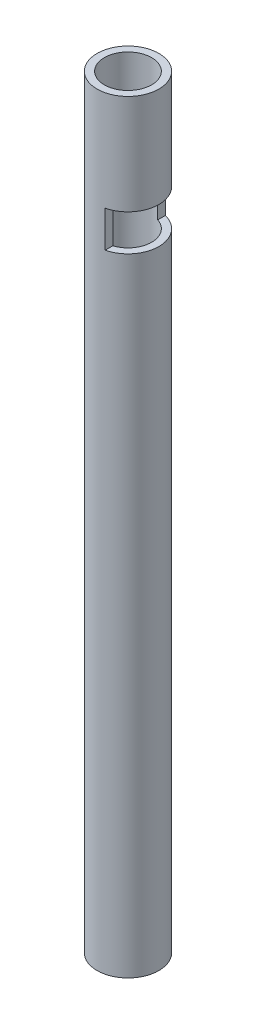
SolidWorks part; units mm, degrees
ref_plane "Alzado" through (0, 0, 0) normal (0, 0, 1) x (1, 0, 0)
ref_plane "Planta" through (0, 0, 0) normal (0, 1, 0) x (1, 0, 0)
ref_plane "Vista lateral" through (0, 0, 0) normal (1, 0, 0) x (0, 0, -1)
sketch "Croquis2" plane through (0, 0, 0) normal (0, 1, 0) x (1, 0, 0)
  circle A0 centre (0, 0) radius 17
  circle A1 centre (0, 0) radius 13
  dimension "D1" = 34
  dimension "D2" = 26
extrude "Saliente-Extruir1" add sketch "Croquis2" along normal blind 420
sketch "Croquis3" plane through (0, 0, 0) normal (0, 0, 1) x (1, 0, 0)
  line L0 (17, 420) -> (-17, 420) construction
  line L1 (4, 345) -> (29, 345)
  line L2 (4, 345) -> (4, 365)
  line L3 (4, 365) -> (29, 365)
  line L4 (29, 345) -> (29, 365)
  line L5 (-17, 420) -> (-17, 0) construction
  dimension "D1" = 75
  dimension "D2" = 365
  dimension "D3" = 21
  dimension "D4" = 25
extrude "Cortar-Extruir1" cut sketch "Croquis3" against normal mid plane 50
